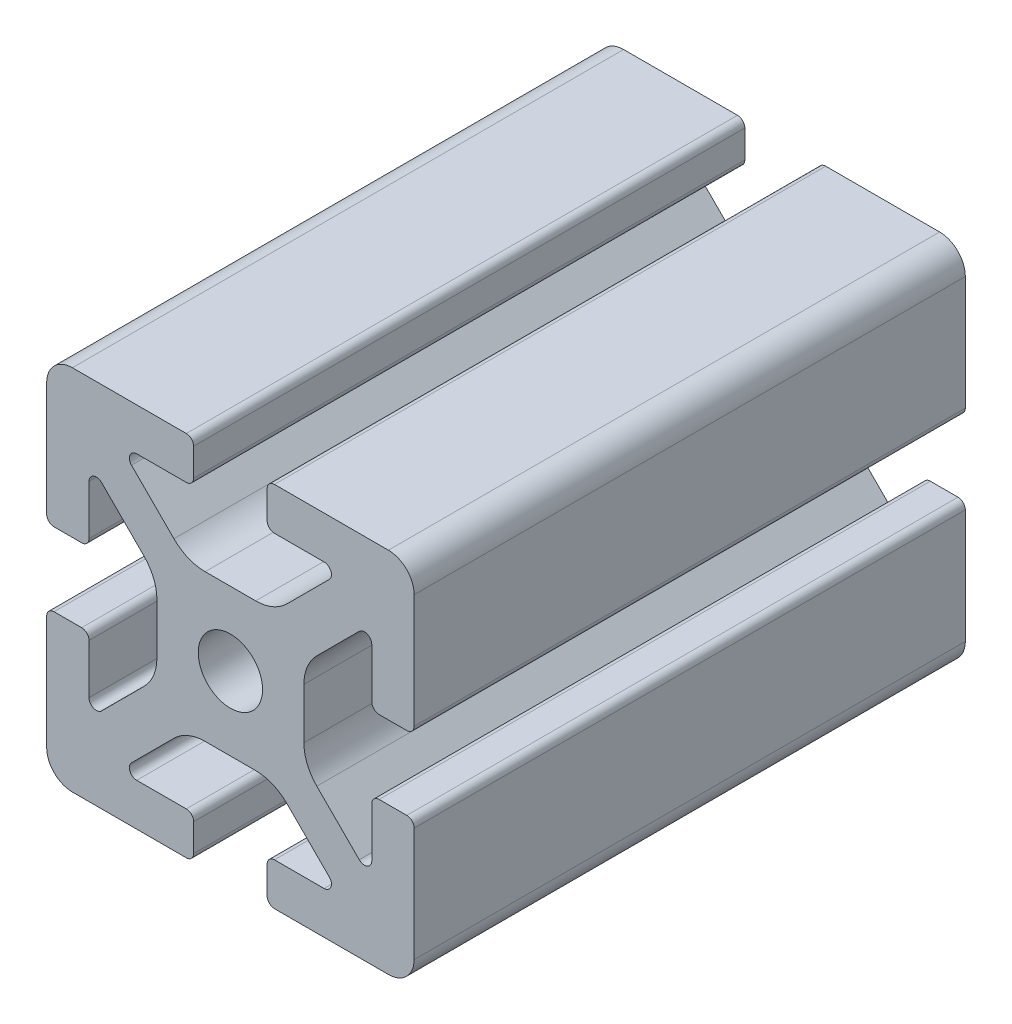
SolidWorks part; units mm, degrees
material "6061-T6 (SS)"
ref_plane "Front Plane" through (0, 0, 0) normal (0, 0, 1) x (1, 0, 0)
ref_plane "Top Plane" through (0, 0, 0) normal (0, 1, 0) x (1, 0, 0)
ref_plane "Right Plane" through (0, 0, 0) normal (1, 0, 0) x (0, 0, -1)
sketch "Sketch2" plane through (0, 0, 0) normal (0, 0, 1) x (1, 0, 0)
  line L0 (0, 20) -> (0, -20) construction
  line L1 (-20, 0) -> (20, 0) construction
  line L2 (4, -20) -> (20, -20)
  line L3 (20, -20) -> (20, -4)
  line L4 (4, -20) -> (4, -15.3907)
  line L5 (4, -15.3907) -> (12.1314, -15.3907)
  line L6 (12.1314, -15.3907) -> (4.7407, -8)
  line L7 (0, 0) -> (20, -20) construction
  line L8 (20, -4) -> (15.3907, -4)
  line L9 (15.3907, -4) -> (15.3907, -12.1314)
  line L10 (15.3907, -12.1314) -> (8, -4.7407)
  line L11 (11.6953, -8.436) -> (8.436, -11.6953) construction
  circle A0 centre (0, 0) radius 3.5
  arc A1 (10.2, -15.3907) -> (10.7657, -14.025) centre (10.2, -14.5907) ccw construction
  point P8 (0, -8)
  point P16 (10.0657, -10.0657)
  dimension "Center Hole Diameter" = 7
  dimension "D3" = 0.8
  dimension "Rail Height" = 40
  dimension "Rail Width" = 40
  dimension "T-Slot Width" = 8
  dimension "Slot Depth" = 12
  dimension "Slot Inner Width" = 22
sketch "Sketch3" plane through (0, 0, 0) normal (1, 0, 0) x (0, 0, -1)
  line L0 (-152.4, -20) -> (152.4, -20) construction
  line L1 (-127, 0) -> (127, 0) construction
  line L2 (0, 20) -> (0, -20) construction
  line L3 (0, 20) -> (0, -20) construction
  point P6 (-127, 0)
  point P8 (127, 0)
  dimension "Length" = 304.8
  dimension "D1" = 25.4
sketch "Sketch4" plane through (0, 0, 0) normal (0, 0, 1) x (1, 0, 0)
  line L0 (4.8, -20) -> (17.2, -20)
  line L1 (4, -20) -> (20, -20) construction
  line L2 (4, -20) -> (4, -15.3907) construction
  line L3 (4, -15.3907) -> (12.1314, -15.3907) construction
  line L4 (4, -16.1907) -> (4, -19.2)
  line L5 (4.8, -15.3907) -> (10.2, -15.3907)
  line L6 (0, -8) -> (2.7525, -8)
  line L7 (12.1314, -15.3907) -> (4.7407, -8) construction
  line L8 (6.1466, -9.4059) -> (10.7657, -14.025)
  line L9 (20, -20) -> (20, -4) construction
  line L10 (15.3907, -12.1314) -> (8, -4.7407) construction
  line L11 (15.3907, -4) -> (15.3907, -12.1314) construction
  line L12 (15.3907, -10.2) -> (15.3907, -4.8)
  line L13 (20, -4) -> (15.3907, -4) construction
  line L14 (16.1907, -4) -> (19.2, -4)
  line L15 (20, -4.8) -> (20, -17.2)
  line L16 (14.025, -10.7657) -> (9.4059, -6.1466)
  line L17 (8, 0) -> (8, -2.7525)
  line L18 (-20, 0) -> (20, 0) construction
  line L19 (0, -8) -> (0, -3.5)
  line L20 (0, 20) -> (0, -20) construction
  line L21 (8, 0) -> (3.5, 0)
  arc A0 (4, -19.2) -> (4.8, -20) centre (4.8, -19.2) ccw
  arc A1 (10.2, -15.3907) -> (10.7657, -14.025) centre (10.2, -14.5907) ccw construction
  arc A2 (4, -16.1907) -> (4.8, -15.3907) centre (4.8, -16.1907) cw
  arc A3 (10.2, -15.3907) -> (10.7657, -14.025) centre (10.2, -14.5907) ccw
  arc A4 (2.7525, -8) -> (6.1466, -9.4059) centre (2.7525, -12.8) cw
  arc A5 (17.2, -20) -> (20, -17.2) centre (17.2, -17.2) ccw
  arc A6 (14.025, -10.7657) -> (15.3907, -10.2) centre (14.5907, -10.2) ccw
  arc A7 (15.3907, -4.8) -> (16.1907, -4) centre (16.1907, -4.8) cw
  arc A8 (19.2, -4) -> (20, -4.8) centre (19.2, -4.8) cw
  arc A9 (9.4059, -6.1466) -> (8, -2.7525) centre (12.8, -2.7525) cw
  circle A10 centre (0, 0) radius 3.5 construction
  arc A11 (0, -3.5) -> (3.5, 0) centre (0, 0) ccw
  dimension "D1" = 2.8
  dimension "D2" = 4.8
extrude "Boss-Extrude1" add sketch "Sketch4" along normal mid plane 60
mirror "Mirror1" about plane through (0, 0, 0) normal (1, 0, 0) of bodies 134
mirror "Mirror2" about plane through (0, 0, 0) normal (0, 1, 0) of bodies 135
equation "\"D3@Sketch2\"=\"T-Slot Width@Sketch2\"*0.1"
equation "\"D1@Sketch4\"=\"D3@Sketch2\"*3.5"
equation "\"D2@Sketch4\"=\"D3@Sketch2\"*6"
equation "\"D1@Boss-Extrude1\"=\"Length@Sketch3\""
